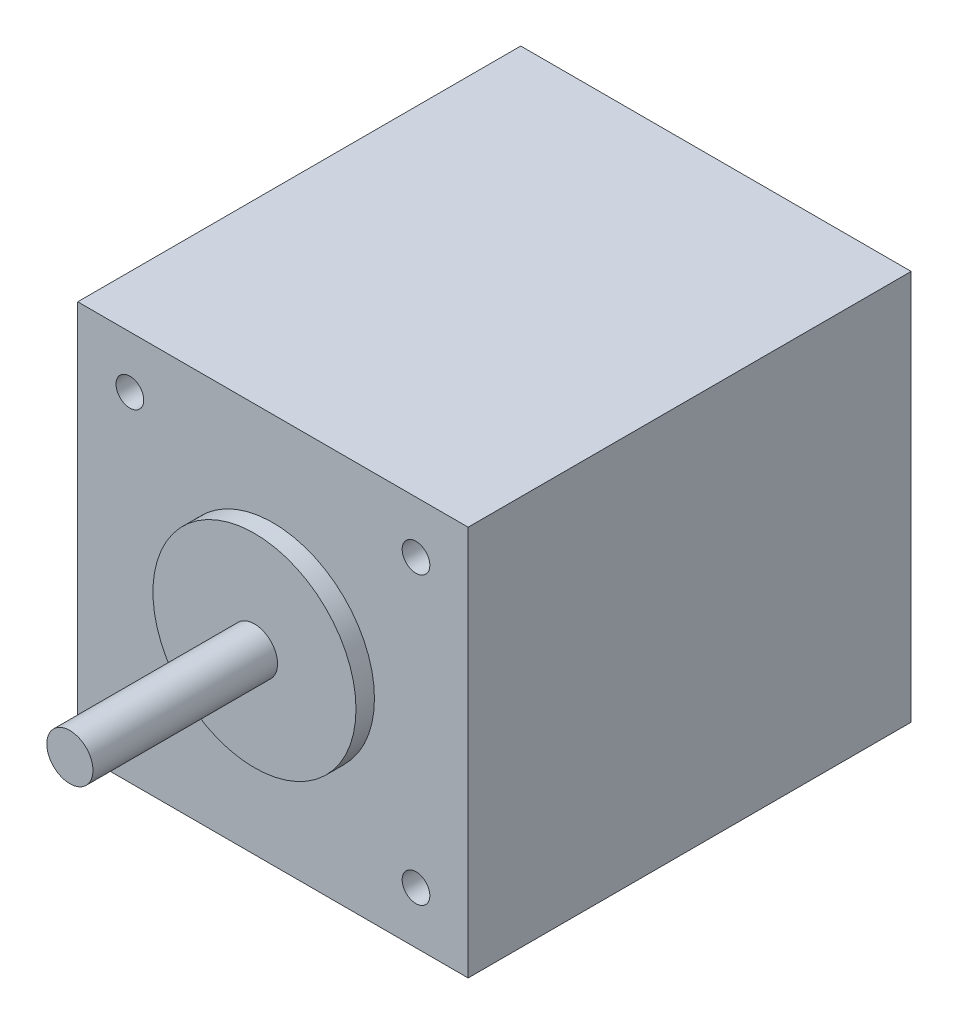
SolidWorks part; units mm, degrees
ref_plane "Plan de face" through (0, 0, 0) normal (0, 0, 1) x (1, 0, 0)
ref_plane "Plan de dessus" through (0, 0, 0) normal (0, 1, 0) x (1, 0, 0)
ref_plane "Plan de droite" through (0, 0, 0) normal (1, 0, 0) x (0, 0, -1)
ref_plane "Plan1" through (21.15, 0, 0) normal (1, 0, 0) x (0, 0, -1)
sketch "Esquisse1" plane through (21.15, 0, 0) normal (1, 0, 0) x (0, 0, -1)
  line L0 (48, -21.15) -> (48, 21.15)
  line L1 (48, 21.15) -> (0, 21.15)
  line L2 (0, 21.15) -> (0, -21.15)
  line L3 (0, -21.15) -> (48, -21.15)
extrude "Boss.-Extru.1" add sketch "Esquisse1" against normal blind 42.3
sketch "Esquisse2" plane through (0, 0, 0) normal (0, 1, 0) x (1, 0, 0)
  line L0 (11, 0) -> (0, 0)
  line L1 (0, 0) -> (0, -22)
  line L2 (0, -22) -> (2.5, -22)
  line L3 (2.5, -22) -> (2.5, -2)
  line L4 (2.5, -2) -> (11, -2)
  line L5 (11, -2) -> (11, 0)
  line L6 (0, 0) -> (0, -22) construction
revolve "Révolution1" add sketch "Esquisse2" angle 360 about L6
hole_wizard "Diamètre du perçage Ø3.0 (3)1" positions "Esquisse4" profile "Esquisse3" hole size "Ø3.0" standard "Ansi Metric"
sketch "Esquisse4" plane through (0, 0, 0) normal (0, 0, 1) x (1, 0, 0)
  point P0 (15.5, 15.5)
  point P1 (15.5, -15.5)
  point P2 (-15.5, 15.5)
  point P3 (-15.5, -15.5)
sketch "Esquisse3" plane through (15.5, 15.5, 0) normal (1, 0, 0) x (0, -1, 0)
  line L0 (0, 0) -> (0, 5)
  line L1 (0, 5) -> (1.5, 5)
  line L2 (1.5, 5) -> (1.5, 0)
  line L5 (1.5, 0) -> (0, 0)
  line L10 (0, 5) -> (-1.5, 5) construction
  line L11 (0, -6.35) -> (0, 107.95) construction
  dimension "Diamètre du perçage" = 3
  dimension "Profondeur du perçage" = 5
  dimension "Angle de pointe" = 180
